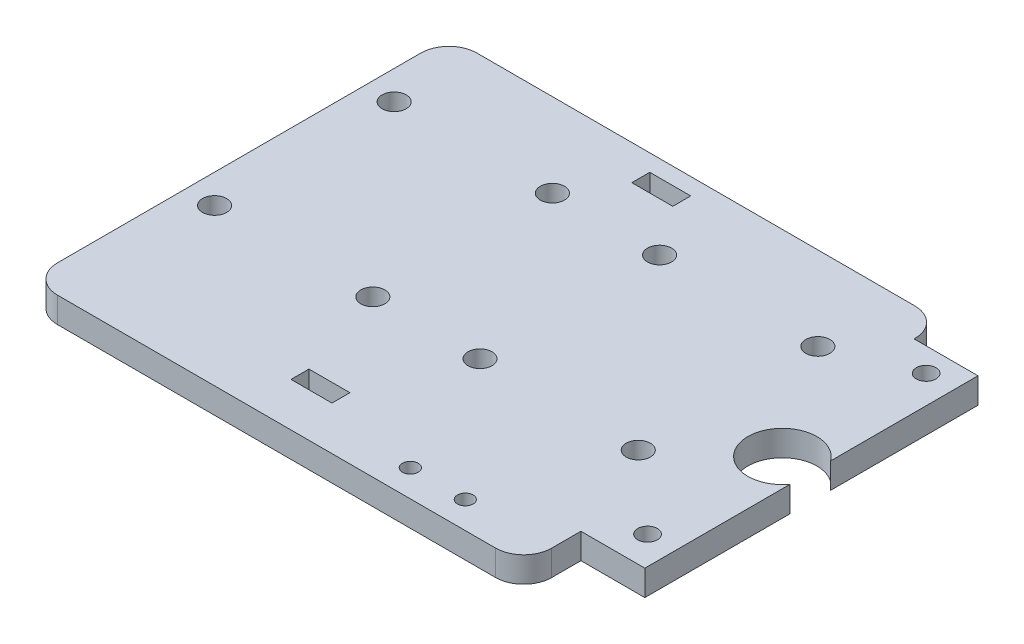
SolidWorks part; units mm, degrees
ref_plane "Front Plane" through (0, 0, 0) normal (0, 0, 1) x (1, 0, 0)
ref_plane "Top Plane" through (0, 0, 0) normal (0, 1, 0) x (1, 0, 0)
ref_plane "Right Plane" through (0, 0, 0) normal (1, 0, 0) x (0, 0, -1)
sketch "Sketch1" plane through (0, 0, 0) normal (0, 1, 0) x (1, 0, 0)
  line L1 (5, 0) -> (83.06, 0)
  line L2 (0, 5) -> (0, 69.73)
  line L3 (5, 74.73) -> (83.06, 74.73)
  line L4 (114.36, 15.2) -> (114.36, 64.57)
  line L5 (88.06, 69.57) -> (109.36, 69.57)
  line L6 (88.06, 69.57) -> (88.06, 69.73)
  line L11 (109.36, 10.2) -> (88.06, 10.2)
  line L12 (88.06, 5) -> (88.06, 10.2)
  line L13 (38.8, 71.73) -> (46.1, 71.73)
  line L14 (38.8, 71.73) -> (38.8, 68.53)
  line L15 (38.8, 68.53) -> (46.1, 68.53)
  line L16 (46.1, 71.73) -> (46.1, 68.53)
  line L17 (38.8, 11) -> (46.1, 11)
  line L18 (38.8, 11) -> (38.8, 7.8)
  line L19 (38.8, 7.8) -> (46.1, 7.8)
  line L20 (46.1, 11) -> (46.1, 7.8)
  circle A0 centre (5.15, 59.83) radius 2.15
  circle A1 centre (33.35, 59.83) radius 2.15
  circle A2 centre (52.45, 59.83) radius 2.15
  circle A3 centre (80.65, 59.83) radius 2.15
  circle A8 centre (5.15, 27.83) radius 2.15
  circle A9 centre (33.35, 27.83) radius 2.15
  circle A10 centre (52.45, 27.83) radius 2.15
  circle A11 centre (80.65, 27.83) radius 2.15
  arc A12 (88.06, 69.73) -> (83.06, 74.73) centre (83.06, 69.73) ccw
  arc A13 (109.36, 69.57) -> (114.36, 64.57) centre (109.36, 64.57) cw
  arc A14 (114.36, 15.2) -> (109.36, 10.2) centre (109.36, 15.2) cw
  arc A15 (83.06, 0) -> (88.06, 5) centre (83.06, 5) ccw
  arc A16 (5, 0) -> (0, 5) centre (5, 5) cw
  arc A17 (0, 69.73) -> (5, 74.73) centre (5, 69.73) cw
  circle A18 centre (94.47, 39.69) radius 6.15
  circle A19 centre (94.45, 65.33) radius 1.75
  circle A20 centre (94.45, 15.69) radius 1.75
  circle A21 centre (63.06, 4.8) radius 1.4
  circle A22 centre (72.86, 4.8) radius 1.4
  point P27 (88.06, 74.73)
  point P30 (114.36, 69.57)
  point P33 (114.36, 10.2)
  point P36 (88.06, 0)
  point P39 (0, 0)
  point P42 (0, 74.73)
  dimension "D3" = 4.3
  dimension "D4" = 4.3
  dimension "D5" = 4.3
  dimension "D6" = 4.3
  dimension "D19" = 5
  dimension "D28" = 12.3
  dimension "D31" = 3.5
  dimension "D32" = 3.5
  dimension "D37" = 2.8
  dimension "D38" = 2.8
  dimension "D1" = 74.73
  dimension "D8" = 14.9
  dimension "D9" = 14.9
  dimension "D10" = 14.9
  dimension "D7" = 14.9
  dimension "D11" = 28.2
  dimension "D12" = 28.2
  dimension "D13" = 19.1
  dimension "D14" = 5.15
  dimension "D16" = 5.16
  dimension "D17" = 26.3
  dimension "D2" = 26.3
  dimension "D18" = 10.2
  dimension "D20" = 7.3
  dimension "D21" = 3.2
  dimension "D22" = 38.8
  dimension "D23" = 7.8
  dimension "D24" = 7.3
  dimension "D25" = 3.2
  dimension "D26" = 0
  dimension "D27" = 3
  dimension "D29" = 19.89
  dimension "D30" = 29.88
  dimension "D34" = 94.45
  dimension "D35" = 9.4
  dimension "D36" = 49.64
  dimension "D33" = 0
  dimension "D39" = 9.8
  dimension "D40" = 4.8
  dimension "D41" = 4.8
  dimension "D42" = 15.2
  dimension "D15" = 2
extrude "Boss-Extrude1" add sketch "Sketch1" along normal blind 4.55
sketch "Sketch2" plane through (0, 4.55, 0) normal (0, 1, 0) x (1, 0, 0)
  line L1 (130.0472, 0) -> (99.45, 0)
  line L2 (130.0472, 0) -> (130.0472, 76.2403)
  line L3 (130.0472, 76.2403) -> (99.45, 76.2403)
  line L4 (99.45, 0) -> (99.45, 76.2403)
  circle A0 centre (94.45, 65.33) radius 1.75 construction
  dimension "D1" = 5
extrude "Cut-Extrude1" cut sketch "Sketch2" against normal through all
equation "\"D4@Sketch1\"=\"D3@Sketch1\""
equation "\"D5@Sketch1\"=\"D4@Sketch1\""
equation "\"D6@Sketch1\"=\"D3@Sketch1\""
equation "\"D8@Sketch1\"=\"D7@Sketch1\""
equation "\"D9@Sketch1\"=\"D7@Sketch1\""
equation "\"D10@Sketch1\"=\"D7@Sketch1\""
equation "\"D12@Sketch1\"=\"D11@Sketch1\""
equation "\"D24@Sketch1\"=\"D20@Sketch1\""
equation "\"D25@Sketch1\"=\"D21@Sketch1\""
equation "\"D41@Sketch1\"=\"D40@Sketch1\""
